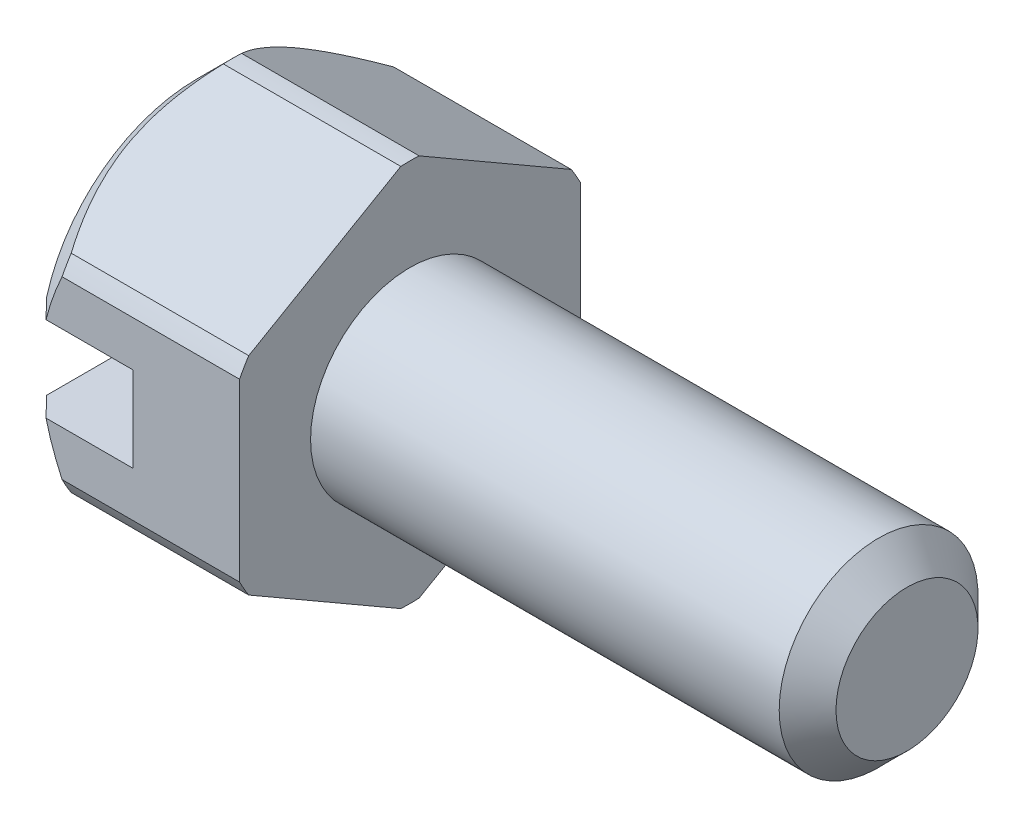
SolidWorks part; units mm, degrees
material "Литая легированная сталь"
ref_plane "Спереди" through (0, 0, 0) normal (0, 0, 1) x (1, 0, 0)
ref_plane "Сверху" through (0, 0, 0) normal (0, 1, 0) x (1, 0, 0)
ref_plane "Справа" through (0, 0, 0) normal (1, 0, 0) x (0, 0, -1)
sketch "Эскиз1" plane through (0, 0, 0) normal (0, 0, 1) x (1, 0, 0)
  line L0 (0, 0) -> (0, 2.7)
  line L1 (0, 2.7) -> (3, 2.7)
  line L2 (3, 2.7) -> (3, 1.4)
  line L3 (3, 1.4) -> (9.6, 1.4)
  line L4 (10, 1) -> (10, 0)
  line L5 (10, 0) -> (0, 0)
  line L6 (-1.2941, 0) -> (13.8463, 0) construction
  line L7 (9.6, 1.4) -> (10, 1)
  point P3 (10, 1.4)
  dimension "D1" = 2.8
  dimension "D2" = 5.4
  dimension "D3" = 3
  dimension "D4" = 10
  dimension "D5" = 0.4
  dimension "D6" = 45
revolve "Повернуть1" add sketch "Эскиз1" angle 360 about L6
cosmetic thread "Условное изображение резьбы1" parameters "D2"=2.0879
sketch "Эскиз2" plane through (0, 0, 0) normal (-1, 0, 0) x (0, 0, 1)
  line L0 (-2.6325, 0.6) -> (2.6325, 0.6)
  line L1 (2.6325, -0.6) -> (-2.6325, -0.6)
  circle A0 centre (0, 0) radius 2.7 construction
  circle M1 centre (0, 0) radius 2.7
  dimension "D1" = 1.2
extrude "Вырез-Вытянуть2" cut sketch "Эскиз2" against normal offset from surface (1.5 mm away) 1.5 contours L1 L0 M1 up to face at (3, 0, 1.4)
chamfer "Фаска1" distance 0.5 angle 45 2 edges at (0, 2.7, 0) (0, -2.7, 0)
sketch "Эскиз4" plane through (3, 0, 0) normal (1, 0, 0) x (0, 0, -1)
  line L1 (0, 2.7713) -> (-2.4, 1.3856)
  line L2 (-2.4, 1.3856) -> (-2.4, -1.3856)
  line L3 (-2.4, -1.3856) -> (0, -2.7713)
  line L4 (0, -2.7713) -> (2.4, -1.3856)
  line L5 (2.4, -1.3856) -> (2.4, 1.3856)
  line L6 (2.4, 1.3856) -> (0, 2.7713)
  circle A0 centre (0, 0) radius 2.4 construction
  circle M2 centre (0, 0) radius 2.7
  dimension "D1" = 4.8
extrude "Вырез-Вытянуть3" cut sketch "Эскиз4" against normal through all contours L6 M2 | L1 M2 | L2 M2 | L3 M2 | L4 M2 | L5 M2
